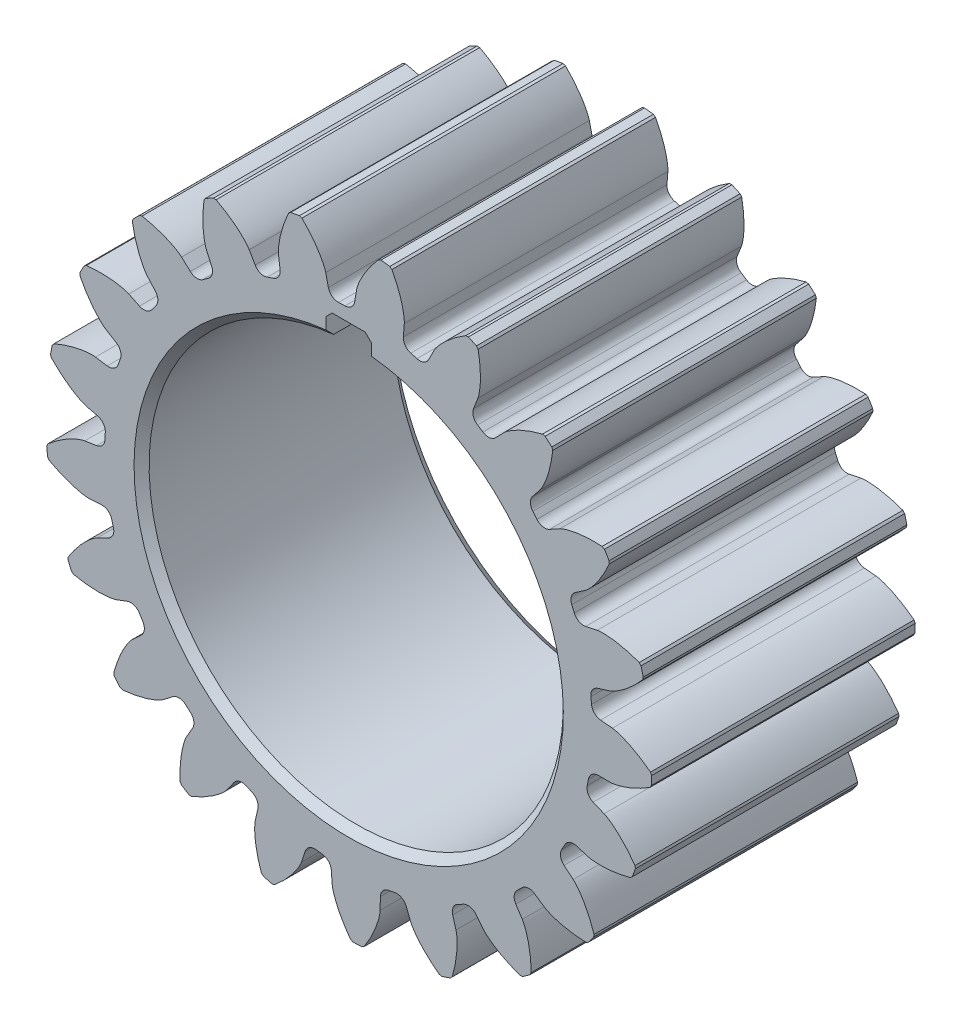
SolidWorks part; units mm, degrees
material "1.6587 (18CrNiMo7-6)"
ref_plane "Front Plane" through (0, 0, 0) normal (0, 0, 1) x (1, 0, 0)
ref_plane "Top Plane" through (0, 0, 0) normal (0, 1, 0) x (1, 0, 0)
ref_plane "Right Plane" through (0, 0, 0) normal (1, 0, 0) x (0, 0, -1)
sketch "Sketch1" plane through (0, 0, 0) normal (0, 0, 1) x (1, 0, 0)
  circle A0 centre (0, 0) radius 36.75 construction
  circle A1 centre (0, 0) radius 32.375
  dimension "D1" = 73.5
  dimension "D2" = 4.375
extrude "Boss-Extrude1" add sketch "Sketch1" along normal blind 35
sketch "Sketch2" plane through (0, 0, 0) normal (0, 0, 1) x (1, 0, 0)
  line L0 (0, 36.75) -> (0, 155.75) construction
  line L1 (-67.7439, 36.75) -> (67.7439, 36.75) construction
  line L2 (0, 36.75) -> (49.8782, 54.9042) construction
  line L3 (0, 36.75) -> (-49.2068, 18.8402) construction
  line L4 (0, 0) -> (0, 32.375) construction
  line L5 (0, 0) -> (36.4805, -4.4427) construction
  line L6 (0, 0) -> (41.7414, -1.9376) construction
  line L7 (34.7215, -4.8001) -> (0, 0) construction
  line L8 (34.7215, -4.8001) -> (33.1428, -4.8001)
  line L9 (0, 0) -> (32.0172, -4.8001) construction
  line L10 (35.0169, 1.5629) -> (33.445, 1.7092)
  arc A1 (31.835, -5.8882) -> (32.2436, 2.9137) centre (0, 0) ccw construction
  circle A2 centre (0, 0) radius 36.75 construction
  arc A3 (31.835, -5.8882) -> (32.2436, 2.9137) centre (0, 0) ccw
  arc A4 (40.1622, -2.6568) -> (40.2356, -1.0752) centre (0, 0) ccw
  circle A5 centre (0, 155.75) radius 119 construction
  circle A8 centre (0, 0) radius 35.0518 construction
  arc A14 (33.1428, -4.8001) -> (31.835, -5.8882) centre (33.1428, -6.1301) ccw
  arc A15 (33.445, 1.7092) -> (32.2436, 2.9137) centre (33.5682, 3.0334) cw
  circle A16 centre (0, 0) radius 32.375 construction
  circle A17 centre (0, 0) radius 40.25 construction
  spline S0 degree 4 poles (34.7215, -4.8001) (34.7341, -4.8001) (34.7691, -4.7996) (34.8355, -4.7962) (34.9436, -4.7875) (35.0811, -4.7717) (35.2585, -4.7459) (35.4668, -4.7086) (35.695, -4.6602) (35.9422, -4.5998) (36.1878, -4.5327) (36.4319, -4.4593) (36.6739, -4.3805) (36.9658, -4.2782) (37.314, -4.1462) (37.7178, -3.9783) (38.1719, -3.772) (38.6302, -3.5448) (39.0773, -3.3074) (39.5241, -3.0518) (39.9529, -2.7933) (40.3929, -2.509) (40.7962, -2.2384) (41.2416, -1.9179) (41.5992, -1.6542) (42.0635, -1.2882) (42.3355, -1.0666) (42.6511, -0.801) (42.7899, -0.6798) (42.8754, -0.6052) knots 0 0 0 0 0 0.005377 0.015084 0.028532 0.04661 0.064855 0.092111 0.119476 0.146842 0.174209 0.201575 0.228941 0.256307 0.307035 0.361767 0.4165 0.471232 0.525964 0.580697 0.635429 0.690161 0.744894 0.799626 0.854358 0.909091 0.954545 1 1 1 1 1 construction
  spline S1 degree 4 poles (34.7215, -4.8001) (34.7341, -4.8001) (34.7691, -4.7996) (34.8355, -4.7962) (34.9436, -4.7875) (35.0811, -4.7717) (35.2585, -4.7459) (35.4668, -4.7086) (35.695, -4.6602) (35.9422, -4.5998) (36.1878, -4.5327) (36.4319, -4.4593) (36.6739, -4.3805) (36.9658, -4.2782) (37.314, -4.1462) (37.7178, -3.9783) (38.1719, -3.772) (38.6302, -3.5448) (39.0773, -3.3074) (39.5216, -3.0532) (39.841, -2.8608) (40.0566, -2.7247) (40.1622, -2.6568) knots 0 0 0 0 0 0.005377 0.015084 0.028532 0.04661 0.064855 0.092111 0.119476 0.146842 0.174209 0.201575 0.228941 0.256307 0.307035 0.361767 0.4165 0.471232 0.525964 0.580697 0.634208 0.634208 0.634208 0.634208 0.634208
  spline S2 degree 4 poles (35.0169, 1.5629) (35.0294, 1.5617) (35.0643, 1.5579) (35.13, 1.5484) (35.2368, 1.5298) (35.3723, 1.5013) (35.5465, 1.4592) (35.7505, 1.4027) (35.9732, 1.3334) (36.2138, 1.2504) (36.4521, 1.1608) (36.6883, 1.0651) (36.922, 0.9642) (37.2032, 0.8353) (37.5376, 0.6716) (37.9241, 0.4671) (38.3572, 0.2195) (38.7925, -0.0491) (39.2156, -0.327) (39.6345, -0.6212) (39.9346, -0.8423) (40.1367, -0.9979) (40.2356, -1.0752) knots 0 0 0 0 0 0.005377 0.015084 0.028532 0.04661 0.064855 0.092111 0.119476 0.146842 0.174209 0.201575 0.228941 0.256307 0.307035 0.361767 0.4165 0.471232 0.525964 0.580697 0.634208 0.634208 0.634208 0.634208 0.634208
  dimension "D1" = 73.5
  dimension "D5" = 20
  dimension "D6" = 70.1036
  dimension "D7" = 2.66
  dimension "D4" = 119
  dimension "D8" = 4.286
  dimension "D2" = 4.375
  dimension "D3" = 3.5
extrude "Boss-Extrude3" add sketch "Sketch2" along normal blind 35
chamfer "Chamfer2" distance 0.2 2 edges at (40.1622, -2.6568, 17.5) (40.2356, -1.0752, 17.5)
pattern_circular "CirPattern3" count 21 over 360 about axis through (0, 0, 35) along (0, 0, -1) of "Boss-Extrude3", "Chamfer2"
sketch "Sketch3" plane through (0, 0, 0) normal (0, 0, 1) x (1, 0, 0)
  line L0 (0, 0) -> (0, 30.7) construction
  line L1 (3, 27.3359) -> (3, 30.7)
  line L2 (-3, 27.3359) -> (-3, 30.7)
  line L4 (3, 30.7) -> (-3, 30.7)
  line L5 (3, 0) -> (3, 30.7) construction
  line L6 (-3, 0) -> (-3, 30.7) construction
  arc A1 (-3, 27.3359) -> (3, 27.3359) centre (0, 0) ccw
  dimension "D1" = 55
  dimension "D2" = 30.7
  dimension "D3" = 3
  dimension "D4" = 3
extrude "Cut-Extrude1" cut sketch "Sketch3" along normal blind 35
chamfer "Chamfer3" distance 1.6 1 edges at (0, -27.5, 0)
chamfer "Chamfer4" distance 1 angle 45 1 edges at (0, -27.5, 35)
chamfer "Chamfer5" distance 0.8 2 edges at (-3, 30.7, 17.5) (3, 30.7, 17.5)
